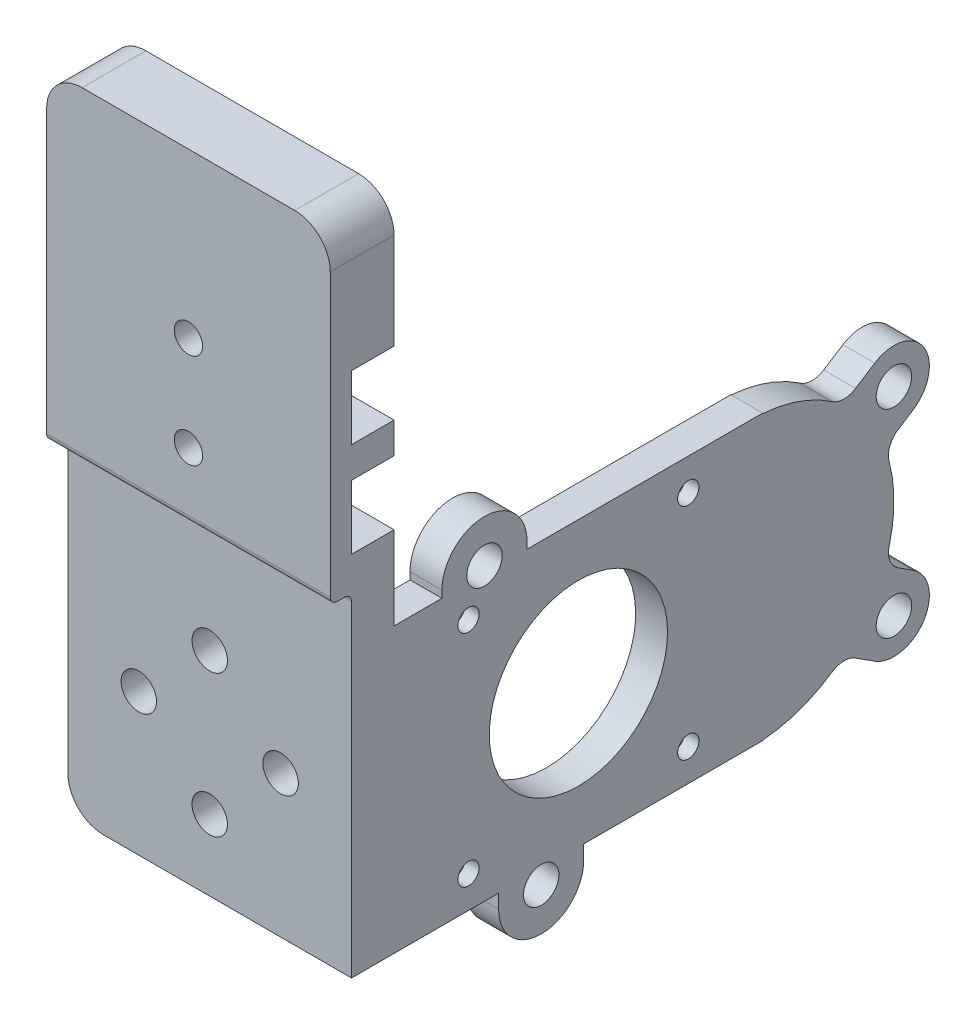
SolidWorks part; units mm, degrees
ref_plane "Front Plane" through (0, 0, 0) normal (0, 0, 1) x (1, 0, 0)
ref_plane "Top Plane" through (0, 0, 0) normal (0, 1, 0) x (1, 0, 0)
ref_plane "Right Plane" through (0, 0, 0) normal (1, 0, 0) x (0, 0, -1)
sketch "Sketch2" plane through (0, 0, 0) normal (0, 0, 1) x (1, 0, 0)
  line L0 (0, 10) -> (0, -10) construction
  line L5 (-20, 20) -> (20, 20)
  line L6 (-20, 20) -> (-20, -20)
  line L7 (-20, -20) -> (20, -20)
  line L8 (20, 20) -> (20, -20)
  line L9 (-10, 0) -> (10, 0) construction
  circle A1 centre (0, 10) radius 2.5
  circle A2 centre (0, -10) radius 2.5
  circle A3 centre (-10, 0) radius 2.5
  circle A4 centre (10, 0) radius 2.5
  dimension "D3" = 5
  dimension "D1" = 20
  dimension "D2" = 20
  dimension "D4" = 40
  dimension "D5" = 40
extrude "Boss-Extrude1" add sketch "Sketch2" against normal blind 6
sketch "Sketch3" plane through (0, 0, -6) normal (0, 0, -1) x (-1, 0, 0)
  line L0 (20, -20) -> (-20, -20) construction
  line L1 (-20, 20) -> (-15.5, 20)
  line L2 (-20, 20) -> (-20, -20)
  line L3 (-20, -20) -> (-15.5, -20)
  line L4 (-15.5, 20) -> (-15.5, -20)
  dimension "D1" = 4.5
extrude "Boss-Extrude2" add sketch "Sketch3" along normal blind 52
sketch "Sketch4" plane through (15.5, 0, 0) normal (-1, 0, 0) x (0, 0, 1)
  line L0 (-6, 0) -> (-58, 0) construction
  line L1 (-6, 20) -> (-6, -20) construction
  line L2 (-58, -20) -> (-58, 20) construction
  circle A0 centre (-32, 0) radius 12.5732
  circle A1 centre (-16.5, 15.5) radius 1.5
  circle A2 centre (-16.5, -15.5) radius 1.5
  circle A3 centre (-47.5, -15.5) radius 1.5
  circle A4 centre (-47.5, 15.5) radius 1.5
  point P19 (-32, 0)
  dimension "D3" = 3
  dimension "D1" = 15.5
  dimension "D4" = 15.5
  dimension "D2" = 4
extrude "Cut-Extrude1" cut sketch "Sketch4" against normal up to next
sketch "Sketch5" plane through (0, 0, -6) normal (0, 0, -1) x (-1, 0, 0)
  circle A0 centre (0, 10) radius 4.5
  circle A2 centre (10, 0) radius 4.5
  circle A3 centre (0, -10) radius 4.5
  circle A4 centre (-10, 0) radius 4.5
  dimension "D1" = 9
extrude "Cut-Extrude2" cut sketch "Sketch5" against normal blind 1.5
sketch "Sketch6" plane through (15.5, 0, 0) normal (-1, 0, 0) x (0, 0, 1)
  circle A0 centre (-16.5, 15.5) radius 3
  circle A1 centre (-47.5, 15.5) radius 3
  circle A2 centre (-47.5, -15.5) radius 3
  circle A3 centre (-16.5, -15.5) radius 3
  dimension "D1" = 6
extrude "Cut-Extrude3" cut sketch "Sketch6" against normal blind 2.5
fillet "Fillet1" radius 5 1 edges at (-20, -20, -3)
sketch "Sketch7" plane through (0, 20, 0) normal (0, 1, 0) x (1, 0, 0)
  line L0 (11.3015, -6) -> (-12.8253, -6)
  line L5 (-12.8253, -6) -> (-12.8253, -4.5)
  line L16 (6.4761, 3.0522) -> (-7.9999, 3.0522)
  line L22 (15.5, 6) -> (-20, 6) construction
  line L23 (6.4761, -4.5) -> (6.4761, -3.0522)
  line L26 (11.3015, 6) -> (11.3015, 4.5)
  line L27 (-12.8253, 3.0522) -> (-12.8253, -3.0522)
  line L28 (11.3015, 3.0522) -> (11.3015, -3.0522)
  line L29 (-7.9999, 4.5) -> (-12.8253, 4.5)
  line L30 (-9.7777, 3.0522) -> (-12.8253, 3.0522)
  line L31 (-7.9999, 4.5) -> (-7.9999, 3.0522)
  line L32 (-9.7777, 3.0522) -> (-9.7777, 1.6022)
  line L33 (8.2539, 1.6022) -> (-9.7777, 1.6022)
  line L34 (8.2539, 3.0522) -> (8.2539, 1.6022)
  line L35 (11.3015, 3.0522) -> (8.2539, 3.0522)
  line L36 (11.3015, 4.5) -> (6.4761, 4.5)
  line L37 (6.4761, 4.5) -> (6.4761, 3.0522)
  line L38 (-12.8253, 6) -> (-12.8253, 4.5)
  line L40 (11.3015, 6) -> (-12.8253, 6)
  line L41 (11.3015, -4.5) -> (6.4761, -4.5)
  line L42 (11.3015, -3.0522) -> (8.2539, -3.0522)
  line L43 (8.2539, -3.0522) -> (8.2539, -1.6022)
  line L44 (8.2539, -1.6022) -> (-9.7777, -1.6022)
  line L45 (-9.7777, -3.0522) -> (-9.7777, -1.6022)
  line L46 (-7.9999, -4.5) -> (-7.9999, -3.0522)
  line L47 (-9.7777, -3.0522) -> (-12.8253, -3.0522)
  line L48 (-7.9999, -4.5) -> (-12.8253, -4.5)
  line L49 (11.3015, -6) -> (11.3015, -4.5)
  line L52 (6.4761, -3.0522) -> (-7.9999, -3.0522)
sketch "Sketch9" plane through (15.5, 0, 0) normal (-1, 0, 0) x (0, 0, 1)
  line L0 (-32.75, -22) -> (-32.75, -18.4344)
  line L3 (-32.75, -18.4344) -> (-20.75, -18.4344)
  line L5 (-20.75, -18.4344) -> (-20.75, -22)
  line L6 (-24.75, 21) -> (-24.75, 17.6037)
  line L9 (-24.75, 17.6037) -> (-12.75, 17.6037)
  line L11 (-12.75, 17.6037) -> (-12.75, 21)
  circle A0 centre (-18.75, 21) radius 2.5
  arc A1 (-12.75, 21) -> (-24.75, 21) centre (-18.75, 21) ccw
  circle A2 centre (-26.75, -22) radius 2.5
  arc A3 (-32.75, -22) -> (-20.75, -22) centre (-26.75, -22) ccw
  arc A4 (-12.9, 22.3333) -> (-24.6, 22.3333) centre (-18.75, 21) ccw construction
  arc A5 (-32.7128, -22.6667) -> (-20.7872, -22.6667) centre (-26.75, -22) ccw construction
sketch "Sketch11" plane through (15.5, 0, 0) normal (-1, 0, 0) x (0, 0, 1)
  line L0 (-56.5, 20) -> (-56.5, -20)
  line L1 (-73.7993, 18.2079) -> (-69.332, 15.3408)
  line L2 (-79.2007, 9.7921) -> (-75.1596, 7.1985)
  line L3 (-79.2007, -9.7921) -> (-75.1596, -7.1985)
  line L4 (-73.7993, -18.2079) -> (-69.332, -15.3408)
  line L6 (-58, 20) -> (0, 20) construction
  line L7 (-58, -20) -> (0, -20) construction
  arc A0 (-56.5, 20) -> (-56.5, -20) centre (-56.5, 0) ccw
  arc A1 (-75.8257, 5.1494) -> (-75.8257, -5.1494) centre (-56.5, 0) ccw construction
  circle A2 centre (-76.5, 14) radius 2.5
  arc A3 (-73.7993, 18.2079) -> (-79.2007, 9.7921) centre (-76.5, 14) ccw
  circle A4 centre (-76.5, -14) radius 2.5
  arc A5 (-79.2007, -9.7921) -> (-73.7993, -18.2079) centre (-76.5, -14) ccw
  line M15 (-58, 20) -> (-58, -20)
extrude "Boss-Extrude6" add sketch "Sketch11" against normal up to surface (4.5 mm away) contours A0 M15 | L1 A3 L2 A0 A2 | L3 A5 L4 A0 A4 up to face at (20, 15.5, -49)
fillet "Fillet2" radius 3 4 edges at (17.75, -15.3408, -69.332) (17.75, 15.3408, -69.332) (17.75, -7.1985, -75.1596) (17.75, 7.1985, -75.1596)
sketch "Sketch15" plane through (15.5, 0, 0) normal (-1, 0, 0) x (0, 0, 1)
  circle A0 centre (-16.5, 15.5) radius 3
  circle A1 centre (-16.5, 15.5) radius 3 construction
extrude "Boss-Extrude15" add sketch "Sketch9" against normal up to surface (4.5 mm away) up to face at (20, 15.5, -49)
sketch "Sketch24" plane through (15.5, 0, 0) normal (-1, 0, 0) x (0, 0, 1)
  circle A0 centre (-18.75, 21) radius 2.5
  circle A1 centre (-26.75, -22) radius 2.5
  arc A2 (-28.25, -20) -> (-25.25, -20) centre (-26.75, -22) ccw construction
  arc A3 (-16.4587, 20) -> (-21.0413, 20) centre (-18.75, 21) ccw construction
extrude "Cut-Extrude11" cut sketch "Sketch24" against normal up to surface (4.5 mm away) up to face at (20, -0.0769, -50.4635)
extrude "Cut-Extrude12" cut sketch "Sketch15" against normal up to surface (2.5 mm away) up to face at (18, 15.0519, -16.5)
sketch "Sketch25" plane through (0, 20, 0) normal (0, 1, 0) x (1, 0, 0)
  line L0 (20, 12.75) -> (20, 0) construction
  line L1 (20, -3) -> (-20, -3)
  line L2 (20, -3) -> (20, 6)
  line L3 (20, 6) -> (-20, 6)
  line L4 (-20, -3) -> (-20, 6)
  line L7 (4.5, 6) -> (-4.5, 6) construction
  line L8 (-20, 6) -> (-20, 0) construction
  dimension "D2" = 9
extrude "Boss-Extrude16" add sketch "Sketch25" along normal blind 52.75
sketch "Sketch28" plane through (0, 0, 3) normal (0, 0, 1) x (1, 0, 0)
  line L0 (20, 72.75) -> (20, 20) construction
  line L1 (-20, 20) -> (20, 20)
  line L2 (-20, 20) -> (-20, 22)
  line L3 (-20, 22) -> (20, 22)
  line L4 (20, 20) -> (20, 22)
  dimension "D1" = 2
extrude "Cut-Extrude15" cut sketch "Sketch28" against normal up to surface (3 mm away) up to face at (12.5, 0, 0)
sketch "Sketch33" plane through (0, 0, 3) normal (0, 0, 1) x (1, 0, 0)
  line L0 (20, 72.75) -> (20, 22) construction
  line L1 (-20, 22) -> (20, 22)
  line L2 (-20, 22) -> (-20, 27)
  line L3 (-20, 27) -> (20, 27)
  line L4 (20, 22) -> (20, 27)
  dimension "D1" = 5
extrude "Cut-Extrude18" cut sketch "Sketch33" against normal up to surface (3 mm away) up to face at (12.5, 0, 0)
fillet "Fillet7" radius 1 2 edges at (0, 27, 0) (0, 27, 3)
sketch "Sketch29" plane through (0, 0, 3) normal (0, 0, 1) x (1, 0, 0)
  line L0 (-20, 72.75) -> (-20, 28) construction
  line L1 (-20, 44.7924) -> (20, 44.7924)
  line L2 (-20, 44.7924) -> (-20, 35.75)
  line L3 (-20, 35.75) -> (20, 35.75)
  line L4 (20, 44.7924) -> (20, 35.75)
  line L5 (20, 72.75) -> (20, 28) construction
  line L8 (20, 22) -> (-20, 22) construction
  line L10 (-20, 51.1424) -> (20, 51.1424)
  line L11 (-20, 51.1424) -> (-20, 60.1848)
  line L12 (-20, 60.1848) -> (20, 60.1848)
  line L13 (20, 51.1424) -> (20, 60.1848)
  dimension "D1" = 9.0424
  dimension "D2" = 13.75
  dimension "D3" = 6.35
fillet "Fillet8" radius 5 2 edges at (-20, 72.75, -1.5) (20, 72.75, -1.5)
sketch "Sketch31" plane through (0, 0, -6) normal (0, 0, -1) x (-1, 0, 0)
  line L0 (20, 67.75) -> (20, -15) construction
  line L1 (-20, 40.7924) -> (20, 40.7924)
  line L2 (-20, 40.7924) -> (-20, 31.75)
  line L3 (-20, 31.75) -> (20, 31.75)
  line L4 (20, 40.7924) -> (20, 31.75)
  line L5 (-20, 67.75) -> (-20, 20) construction
  line L6 (-20, 22) -> (20, 22) construction
  line L7 (-20, 54.1848) -> (20, 54.1848)
  line L8 (-20, 54.1848) -> (-20, 45.1424)
  line L9 (-20, 45.1424) -> (20, 45.1424)
  line L10 (20, 54.1848) -> (20, 45.1424)
  dimension "D1" = 9.0424
  dimension "D2" = 4.35
  dimension "D3" = 9.0424
  dimension "D4" = 9.75
extrude "Cut-Extrude16" cut sketch "Sketch31" against normal blind 6
sketch "Sketch32" plane through (0, 0, 0) normal (0, 0, -1) x (-1, 0, 0)
  line L0 (-20, 54.1848) -> (-20, 45.1424) construction
  line L1 (20, 54.1848) -> (-20, 54.1848) construction
  line L2 (-20, 40.7924) -> (-20, 31.75) construction
  line L3 (20, 40.7924) -> (-20, 40.7924) construction
  circle A0 centre (0, 49.6636) radius 2
  circle A1 centre (0, 36.2712) radius 2
  point P6 (-20, 49.6636)
  point P9 (0, 54.1848)
  point P13 (-20, 36.2712)
  point P16 (0, 40.7924)
  dimension "D1" = 4
  dimension "D2" = 4
extrude "Cut-Extrude17" cut sketch "Sketch32" against normal through all
